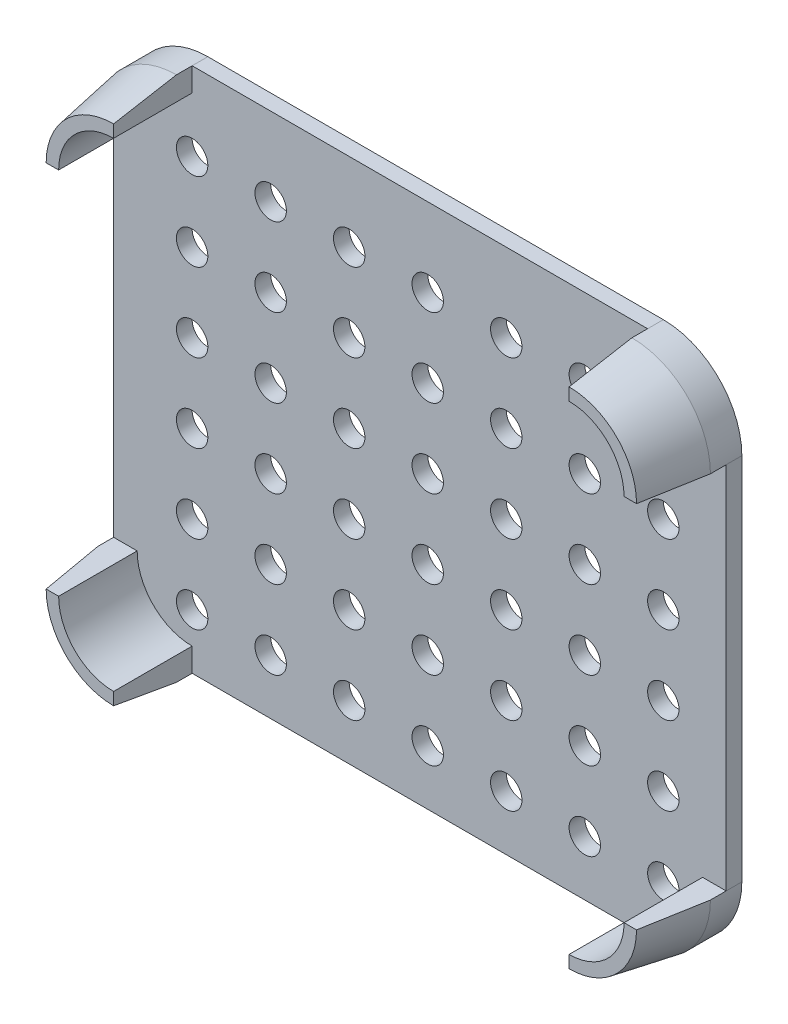
SolidWorks part; units mm, degrees
ref_plane "Plan de face" through (0, 0, 0) normal (0, 0, 1) x (1, 0, 0)
ref_plane "Plan de dessus" through (0, 0, 0) normal (0, 1, 0) x (1, 0, 0)
ref_plane "Plan de droite" through (0, 0, 0) normal (1, 0, 0) x (0, 0, -1)
sketch "Esquisse1" plane through (0, 0, 0) normal (0, 0, 1) x (1, 0, 0)
  line L0 (10, 57) -> (68, 57) construction
  line L1 (10, 0) -> (68, 0)
  line L2 (0, 10) -> (0, 57)
  line L3 (10, 67) -> (68, 67)
  line L4 (78, 10) -> (78, 57)
  line L5 (68, 57) -> (68, 10) construction
  line L6 (68, 10) -> (9.4205, 10) construction
  line L7 (9.4205, 10) -> (10, 57) construction
  arc A0 (10, 0) -> (0, 10) centre (10, 10) cw
  arc A1 (68, 67) -> (78, 57) centre (68, 57) cw
  arc A2 (68, 0) -> (78, 10) centre (68, 10) ccw
  arc A3 (10, 67) -> (0, 57) centre (10, 57) ccw
  circle A4 centre (10, 57) radius 2
  circle A5 centre (20, 57) radius 2
  circle A6 centre (30, 57) radius 2
  circle A7 centre (40, 57) radius 2
  circle A8 centre (50, 57) radius 2
  circle A9 centre (60, 57) radius 2
  circle A10 centre (70, 57) radius 2
  circle A11 centre (20, 47) radius 2
  circle A12 centre (30, 47) radius 2
  circle A13 centre (40, 47) radius 2
  circle A14 centre (50, 47) radius 2
  circle A15 centre (60, 47) radius 2
  circle A16 centre (70, 47) radius 2
  circle A17 centre (20, 37) radius 2
  circle A18 centre (30, 37) radius 2
  circle A19 centre (40, 37) radius 2
  circle A20 centre (50, 37) radius 2
  circle A21 centre (60, 37) radius 2
  circle A22 centre (70, 37) radius 2
  circle A23 centre (20, 27) radius 2
  circle A24 centre (30, 27) radius 2
  circle A25 centre (40, 27) radius 2
  circle A26 centre (50, 27) radius 2
  circle A27 centre (60, 27) radius 2
  circle A28 centre (70, 27) radius 2
  circle A29 centre (20, 17) radius 2
  circle A30 centre (30, 17) radius 2
  circle A31 centre (40, 17) radius 2
  circle A32 centre (50, 17) radius 2
  circle A33 centre (60, 17) radius 2
  circle A34 centre (70, 17) radius 2
  circle A35 centre (20, 7) radius 2
  circle A36 centre (30, 7) radius 2
  circle A37 centre (40, 7) radius 2
  circle A38 centre (50, 7) radius 2
  circle A39 centre (60, 7) radius 2
  circle A40 centre (70, 7) radius 2
  circle A41 centre (10, 47) radius 2
  circle A42 centre (10, 37) radius 2
  circle A43 centre (10, 27) radius 2
  circle A44 centre (10, 17) radius 2
  circle A45 centre (10, 7) radius 2
  point P7 (0, 0)
  dimension "D1" = 10
  dimension "D2" = 7
  dimension "D3" = 6
extrude "Boss.-Extru.1" add sketch "Esquisse1" along normal blind 2 contours A4 | L2 A3 L3 A1 L4 A2 L1 A0 | A6 | A7 | A8
sketch "Esquisse2" plane through (0, 0, 2) normal (0, 0, 1) x (1, 0, 0)
  line L0 (10, 67) -> (10, 64)
  line L2 (0, 10) -> (3, 10)
  line L3 (75, 10) -> (78, 10)
  line L4 (68, 0) -> (68, 3)
  line L6 (78, 57) -> (75, 57)
  line L7 (3, 57) -> (0, 57)
  line L8 (10, 3) -> (10, 0)
  line L9 (68, 64) -> (68, 67)
  arc A0 (10, 67) -> (0, 57) centre (10, 57) ccw
  arc A1 (0, 10) -> (10, 0) centre (10, 10) ccw
  arc A2 (68, 0) -> (78, 10) centre (68, 10) ccw
  arc A3 (78, 57) -> (68, 67) centre (68, 57) ccw
  arc A4 (75, 57) -> (68, 64) centre (68, 57) ccw
  arc A5 (10, 64) -> (3, 57) centre (10, 57) ccw
  arc A6 (3, 10) -> (10, 3) centre (10, 10) ccw
  arc A7 (68, 3) -> (75, 10) centre (68, 10) ccw
  circle A9 centre (10, 57) radius 10 construction
  circle A10 centre (10, 57) radius 7 construction
  circle A11 centre (68, 57) radius 10 construction
  circle A12 centre (68, 57) radius 7 construction
  circle A13 centre (68, 10) radius 7 construction
  circle A14 centre (68, 10) radius 10 construction
  circle A15 centre (10, 10) radius 10 construction
  circle A16 centre (10, 10) radius 7 construction
  point P1 (17, 57)
  point P4 (17, 10)
  point P10 (75, 57)
  point P13 (75, 10)
  point P19 (77.563, 12.9237)
  point P32 (19.563, 59.9237)
  point P39 (77.563, 59.9237)
  point P43 (19.563, 12.9237)
  dimension "D1" = 3
extrude "Boss.-Extru.2" add sketch "Esquisse2" along normal blind 10
chamfer "Chanfrein1" distance 8 angle 10 4 edges at (75.0711, 2.9289, 12) (2.9289, 2.9289, 12) (75.0711, 64.0711, 12) (2.9289, 64.0711, 12)
